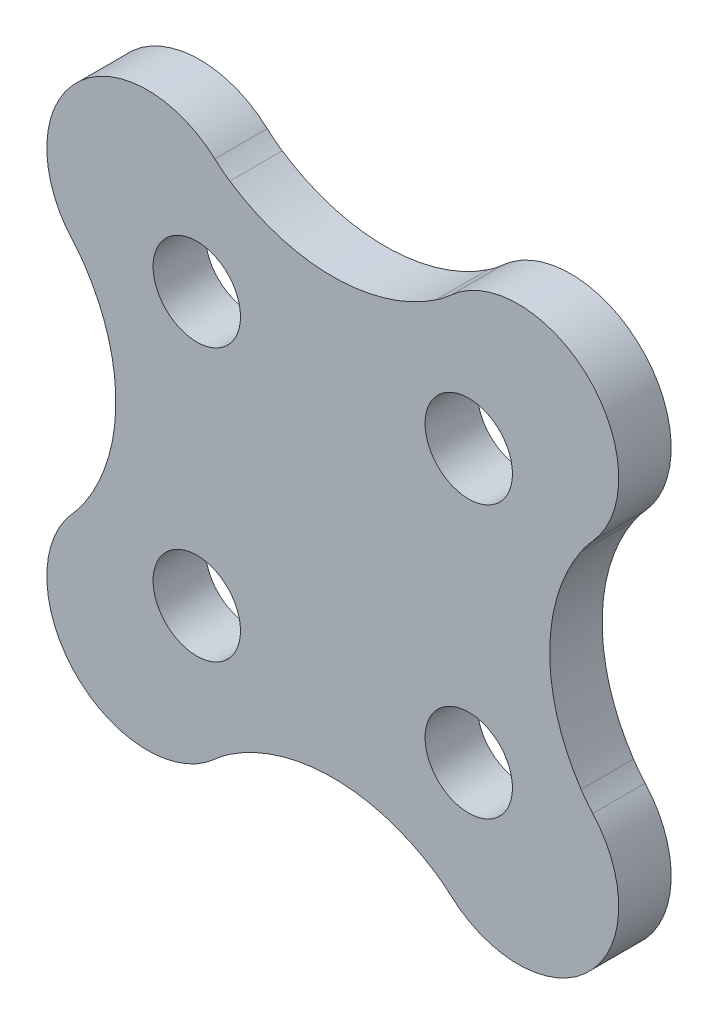
SolidWorks part; units mm, degrees
ref_plane "前视基准面" through (0, 0, 0) normal (0, 0, 1) x (1, 0, 0)
ref_plane "上视基准面" through (0, 0, 0) normal (0, 1, 0) x (1, 0, 0)
ref_plane "右视基准面" through (0, 0, 0) normal (1, 0, 0) x (0, 0, -1)
sketch "Model" plane through (0, 0, 0) normal (0, 0, 1) x (1, 0, 0)
  circle A0 centre (18.2961, 16.99) radius 1
  circle A1 centre (12.0735, 16.99) radius 1
  circle A2 centre (12.0735, 10.7674) radius 1
  circle A3 centre (18.2961, 10.7674) radius 1
  arc A4 (12.4857, 19.8265) -> (12.8286, 19.5586) centre (14.499, 22.0506) ccw
  arc A5 (12.8286, 19.5586) -> (17.5409, 19.5586) centre (15.1848, 23.0737) ccw
  arc A6 (17.5409, 19.5586) -> (17.8839, 19.8265) centre (15.8706, 22.0506) ccw
  arc A7 (21.1326, 16.5778) -> (17.8839, 19.8265) centre (19.4274, 18.1213) ccw
  arc A8 (21.1326, 16.5778) -> (20.8647, 16.2348) centre (23.3567, 14.5645) ccw
  arc A9 (20.8647, 16.2348) -> (20.8647, 11.5226) centre (24.3798, 13.8787) ccw
  arc A10 (20.8647, 11.5226) -> (21.1326, 11.1796) centre (23.3567, 13.1929) ccw
  arc A11 (17.8839, 7.9309) -> (21.1326, 11.1796) centre (19.4274, 9.6361) ccw
  arc A12 (17.8839, 7.9309) -> (17.5409, 8.1988) centre (15.8706, 5.7068) ccw
  arc A13 (17.5409, 8.1988) -> (12.8286, 8.1988) centre (15.1848, 4.6837) ccw
  arc A14 (12.8286, 8.1988) -> (12.4857, 7.9309) centre (14.499, 5.7068) ccw
  arc A15 (12.4857, 19.8265) -> (9.237, 16.5778) centre (10.9421, 18.1213) ccw
  arc A16 (9.5049, 16.2348) -> (9.237, 16.5778) centre (7.0129, 14.5645) ccw
  arc A17 (9.5049, 11.5226) -> (9.5049, 16.2348) centre (5.9898, 13.8787) ccw
  arc A18 (9.237, 11.1796) -> (9.5049, 11.5226) centre (7.0129, 13.1929) ccw
  arc A19 (9.237, 11.1796) -> (12.4857, 7.9309) centre (10.9421, 9.6361) ccw
extrude "凸台-拉伸1" add sketch "Model" along normal blind 1.2 contours A4 A5 A6 A7 A8 A9 A10 A11 A12 A13 A14 A19 A18 A17 A16 A15 | A3 | A2 | A1 | A0
